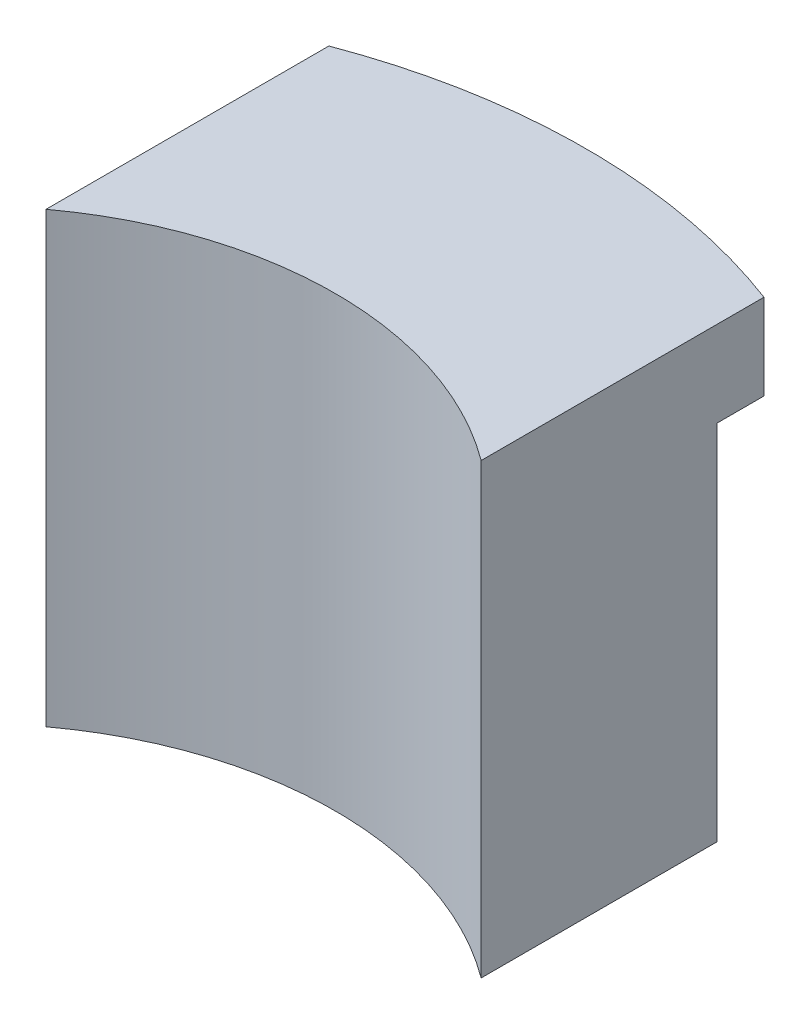
SolidWorks part; units mm, degrees
ref_plane "Front Plane" through (0, 0, 0) normal (0, 0, 1) x (1, 0, 0)
ref_plane "Top Plane" through (0, 0, 0) normal (0, 1, 0) x (1, 0, 0)
ref_plane "Right Plane" through (0, 0, 0) normal (1, 0, 0) x (0, 0, -1)
sketch "Sketch1" plane through (0, 0, 0) normal (0, 1, 0) x (1, 0, 0)
  line L1 (-15, 39.7649) -> (-15, 20.2649)
  line L2 (15, 39.7649) -> (15, 20.2649)
  arc A1 (-15, 39.7649) -> (15, 39.7649) centre (0, 0) cw
  arc A3 (-15, 20.2649) -> (15, 20.2649) centre (0, 0) cw
  dimension "D1" = 19.5
  dimension "D4" = 42.5
  dimension "D2" = 30
  dimension "D3" = 19.5
extrude "Boss-Extrude2" add sketch "Sketch1" along normal blind 2
sketch "Sketch16" plane through (0, 0, 0) normal (0, -1, 0) x (1, 0, 0)
  line L0 (15, -20.2649) -> (15, -39.7649) construction
  line L1 (-15, -20.2649) -> (-15, -39.7649)
  line L2 (15, -20.2649) -> (15, -39.7649)
  line L3 (-13, -23.9064) -> (-13, -38.3569)
  line L4 (13, -23.9064) -> (13, -38.3569)
  arc A0 (-15, -20.2649) -> (15, -20.2649) centre (0, 0) ccw
  arc A1 (-15, -39.7649) -> (15, -39.7649) centre (0, 0) ccw
  arc A4 (-13, -23.9064) -> (13, -23.9064) centre (0, 0) ccw
  arc A5 (-13, -38.3569) -> (13, -38.3569) centre (0, 0) ccw
  arc M1 (-15, -39.7649) -> (15, -39.7649) centre (0, 0) ccw
  line M2 (15, -39.7649) -> (15, -20.2649)
  arc M3 (15, -20.2649) -> (-15, -20.2649) centre (0, 0) cw
  line M4 (-15, -20.2649) -> (-15, -39.7649)
  dimension "D3" = 2
  dimension "D4" = 2
extrude "Boss-Extrude9" add sketch "Sketch16" along normal blind 3 contours A5 L3 A4 L4 M4 M1 M2 M3
sketch "Sketch17" plane through (0, -3, 0) normal (0, -1, 0) x (1, 0, 0)
  line L0 (15, -39.7649) -> (15, -20.2649) construction
  line L1 (-14.5, -21.2339) -> (-14.5, -39.4176)
  line L2 (14.5, -21.2339) -> (14.5, -39.4176)
  line L3 (-15, -20.2649) -> (-15, -39.7649) construction
  arc A0 (-15, -20.2649) -> (15, -20.2649) centre (0, 0) ccw
  arc A1 (-15, -39.7649) -> (15, -39.7649) centre (0, 0) ccw
  arc A4 (-14.5, -21.2339) -> (14.5, -21.2339) centre (0, 0) ccw
  arc A5 (-14.5, -39.4176) -> (14.5, -39.4176) centre (0, 0) ccw
  line M9 (-15, -20.2649) -> (-15, -39.7649)
  arc M10 (-15, -39.7649) -> (15, -39.7649) centre (0, 0) ccw
  line M11 (15, -39.7649) -> (15, -20.2649)
  arc M12 (15, -20.2649) -> (-15, -20.2649) centre (0, 0) cw
  dimension "D1" = 0.5
  dimension "D2" = 0.5
  dimension "D3" = 0.5
  dimension "D4" = 0.5
extrude "Boss-Extrude10" add sketch "Sketch17" along normal blind 0.9 contours A5 L1 A4 L2 M12 M9 M10 M11
sketch3d "3DSketch3" plane through (0, 0, 0) normal (0, 0, 1) x (1, 0, 0)
  dimension "D1" = 50
sketch "Sketch20" plane through (0, 0, -50) normal (0, 0, 1) x (1, 0, 0)
  line L0 (-15, -3.9) -> (15, -3.9) construction
  circle A0 centre (0, -3.9) radius 3.25
  dimension "D1" = 6.5
extrude "Cut-Extrude14" cut sketch "Sketch20" along normal blind 20.9
sketch "Sketch21" plane through (0, -3, 0) normal (0, -1, 0) x (1, 0, 0)
  line L0 (15, -39.7649) -> (15, -20.2649) construction
  line L1 (15, -35.6149) -> (-15, -35.6149)
  line L2 (15, -35.6149) -> (15, -18.7631)
  line L3 (15, -18.7631) -> (-15, -18.7631)
  line L4 (-15, -35.6149) -> (-15, -18.7631)
  dimension "D1" = 15.35
extrude "Cut-Extrude15" cut sketch "Sketch21" along normal blind 1
sketch "Sketch22" plane through (0, -3, 0) normal (0, -1, 0) x (1, 0, 0)
  line L0 (-15, -20.2649) -> (-15, -35.6149) construction
  line L1 (-13, -23.9064) -> (-13, -38.3569) construction
  line L2 (15, -20.2649) -> (15, -35.6149)
  line L3 (15, -35.6149) -> (13, -35.6149)
  line L4 (13, -23.9064) -> (13, -38.3569) construction
  line L5 (13, -35.6149) -> (13, -23.9064)
  line L6 (-13, -23.9064) -> (-13, -35.6149)
  line L7 (-13, -23.9064) -> (-13, -38.3569) construction
  line L8 (-13, -35.6149) -> (-15, -35.6149)
  line L9 (-15, -35.6149) -> (-15, -20.2649)
  arc A0 (15, -20.2649) -> (-15, -20.2649) centre (0, 0) cw
  arc A1 (13, -23.9064) -> (-13, -23.9064) centre (0, 0) cw
extrude "Boss-Extrude11" add sketch "Sketch22" along normal blind 25
sketch "Sketch23" plane through (0, 0, -35.6149) normal (0, 0, -1) x (-1, 0, 0)
  line L0 (-13, -28) -> (-15, -28) construction
  line L1 (-15, -3.9) -> (-14.5, -3.9)
  line L2 (-15, -3.9) -> (-15, -28)
  line L3 (-15, -28) -> (-14.5, -28)
  line L4 (-14.5, -3.9) -> (-14.5, -28)
  line L5 (15, -28) -> (13, -28) construction
  line L6 (15, -3.9) -> (14.5, -3.9)
  line L7 (15, -3.9) -> (15, -28)
  line L8 (15, -28) -> (14.5, -28)
  line L9 (14.5, -3.9) -> (14.5, -28)
  dimension "D1" = 0.5
  dimension "D2" = 0.5
extrude "Boss-Extrude12" add sketch "Sketch23" along normal blind 0.9
sketch "Sketch26" plane through (0, -28, 0) normal (0, -1, 0) x (1, 0, 0)
  line L0 (15, -36.5149) -> (15, -20.2649)
  line L1 (15, -36.5149) -> (14.5, -36.5149)
  line L2 (-15, -20.2649) -> (-15, -36.5149) construction
  line L3 (14.5, -36.5149) -> (14.5, -21.2339)
  line L4 (-15, -20.2649) -> (-15, -36.5149)
  line L5 (-15, -36.5149) -> (-14.5, -36.5149)
  line L6 (-14.5, -36.5149) -> (-14.5, -21.2339)
  arc A0 (15, -20.2649) -> (-15, -20.2649) centre (0, 0) cw
  arc A1 (14.5, -21.2339) -> (-14.5, -21.2339) centre (0, 0) cw
  dimension "D1" = 0.5
extrude "Boss-Extrude13" add sketch "Sketch26" along normal blind 0.9
